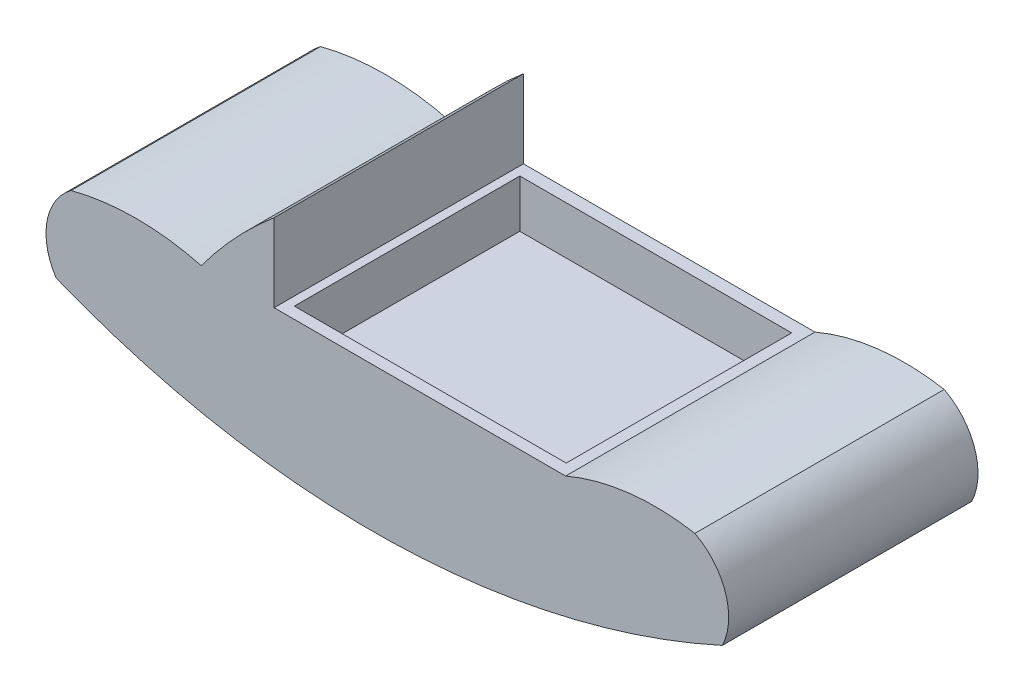
SolidWorks part; units mm, degrees
ref_plane "Front Plane" through (0, 0, 0) normal (0, 0, 1) x (1, 0, 0)
ref_plane "Top Plane" through (0, 0, 0) normal (0, 1, 0) x (1, 0, 0)
ref_plane "Right Plane" through (0, 0, 0) normal (1, 0, 0) x (0, 0, -1)
sketch "Sketch2" plane through (0, 0, 0) normal (0, 0, 1) x (1, 0, 0)
  line L0 (0, 0) -> (-88.9, 0)
  line L1 (0, 0) -> (88.9, 0)
  line L2 (88.9, 0) -> (88.647, -1.1384)
  line L3 (-53.34, 38.0747) -> (-53.34, 0)
  arc A0 (-88.9, 0) -> (-53.34, 38.0747) centre (90.5628, -131.9668) cw
  arc A1 (-88.9, 0) -> (-152.4, 0) centre (-120.65, -121.0409) ccw
  arc A2 (88.9, 0) -> (151.9789, 7.3012) centre (132.6379, -101.7378) cw
  arc A3 (-152.4, 0) -> (-159.7367, -40.64) centre (-134.7142, -24.175) ccw
  arc A4 (151.9789, 7.3012) -> (165.3833, -33.3388) centre (137.7432, -19.9248) cw
  arc A5 (-159.7367, -40.64) -> (165.3833, -33.3388) centre (-5.692, 342.1933) ccw
  point P17 (0, 0)
  point P18 (0, 0)
  point P19 (-96.1355, -1.6444)
  point P20 (0, 0)
  dimension "D1" = 63.5
  dimension "D2" = 63.5
  dimension "D3" = 40.64
  dimension "1.6" = 40.64
  dimension "D4" = 35.56
  dimension "D5" = 325.12
  dimension "D6" = 88.9
  dimension "D7" = 88.9
extrude "Boss-Extrude2" add sketch "Sketch2" along normal blind 121.666
sketch "Sketch4" plane through (0, 0, 0) normal (0, 1, 0) x (1, 0, 0)
  line L0 (83.5621, -116.0473) -> (83.5621, -6.0426)
  line L1 (83.5621, -6.0426) -> (-49.0913, -6.0426)
  line L2 (-49.0913, -6.0426) -> (-49.0913, -116.0473)
  line L3 (-49.0913, -116.0473) -> (83.5621, -116.0473)
  point P2 (-45.0557, -116.0473)
extrude "Cut-Extrude1" cut sketch "Sketch4" against normal blind 23.368 and the other way blind 34.29 contours L3 L0 L1 L2
